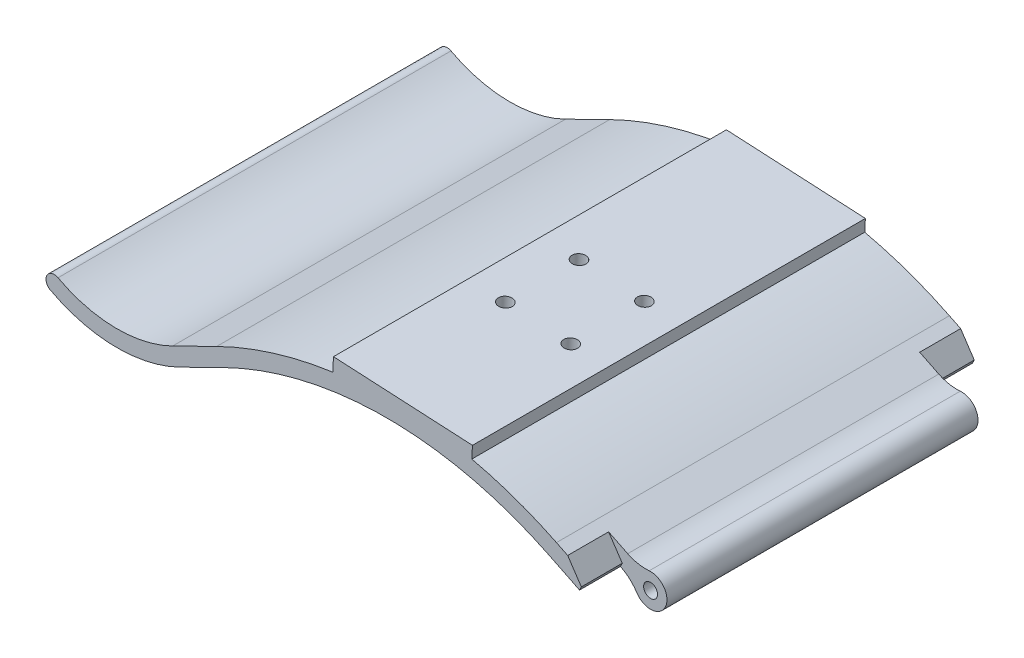
SolidWorks part; units mm, degrees
material "ABS"
ref_plane "Front" through (0, 0, 0) normal (0, 0, 1) x (1, 0, 0)
ref_plane "Top" through (0, 0, 0) normal (0, 1, 0) x (1, 0, 0)
ref_plane "Right" through (0, 0, 0) normal (1, 0, 0) x (0, 0, -1)
sketch "Croquis1" plane through (0, 0, 0) normal (0, 0, 1) x (1, 0, 0)
  line L0 (-39.7374, -9.2477) -> (-50.5044, -14.546)
  line L4 (-80.2705, -10.5153) -> (-82.1489, -14.0467) construction
  line L5 (0, 0) -> (33.2564, 0) construction
  line L6 (0, 22.0797) -> (0, 0) construction
  line L9 (-41.5035, -5.6587) -> (-52.2705, -10.957)
  line L10 (-41.5035, -5.6587) -> (-39.7374, -9.2477) construction
  line L11 (41.5035, -5.6587) -> (39.7374, -9.2477) construction
  line L12 (52.2705, -10.957) -> (50.5044, -14.546) construction
  line L13 (41.5035, -5.6587) -> (52.2705, -10.957)
  line L14 (39.7374, -9.2477) -> (50.5044, -14.546)
  line L15 (-80.2705, -10.5153) -> (-96.9406, -1.6482) construction
  circle A8 centre (54.4956, -14.281) radius 1.7
  arc A12 (52.2705, -10.957) -> (50.5044, -14.546) centre (54.4956, -14.281) cw
  arc A14 (-41.5035, -5.6587) -> (41.5035, -5.6587) centre (0, -90) cw
  arc A15 (-39.7374, -9.2477) -> (39.7374, -9.2477) centre (0, -90) cw
  arc A16 (-52.2705, -10.957) -> (-80.2705, -10.5153) centre (-65.839, 16.6161) cw
  arc A17 (-50.5044, -14.546) -> (-82.1489, -14.0467) centre (-65.839, 16.6161) cw
  arc A18 (-80.2705, -10.5153) -> (-82.1489, -14.0467) centre (-81.2097, -12.281) ccw
  dimension "D1" = 4
  dimension "D3" = 3.4
  dimension "D4" = 90
  dimension "D6" = 28
  dimension "D7" = 105
  dimension "D8" = 2
  dimension "D2" = 4
  dimension "D5" = 12
extrude "Saliente-Extruir1" add sketch "Croquis1" along normal mid plane 96
fillet "Redondeo1" radius 10 2 edges at (50.5044, -14.546, 0) (52.2705, -10.957, 0)
sketch "Croquis3" plane through (0, 0, 48) normal (0, 0, 1) x (1, 0, 0)
  line L0 (48.9085, -9.3026) -> (47.1424, -12.8916)
  arc A0 (51.1332, -16.4476) -> (47.1424, -12.8916) centre (42.7271, -21.8641) ccw construction
  arc A1 (48.9085, -9.3026) -> (54.1608, -10.295) centre (53.3238, -0.3301) ccw construction
  arc A2 (51.1332, -16.4476) -> (54.1608, -10.295) centre (54.4956, -14.281) ccw construction
  arc A3 (51.1332, -16.4476) -> (47.1424, -12.8916) centre (42.7271, -21.8641) ccw
  arc A4 (48.9085, -9.3026) -> (54.1608, -10.295) centre (53.3238, -0.3301) ccw
  arc A5 (51.1332, -16.4476) -> (54.1608, -10.295) centre (54.4956, -14.281) ccw
extrude "Cortar-Extruir1" cut sketch "Croquis3" against normal blind 10
mirror "Simetría1" about plane through (0, 0, 0) normal (0, 0, 1) of "Cortar-Extruir1"
chamfer "Chaflán1" distance 3 angle 60 2 edges at (48.9085, -9.3026, -43) (48.9085, -9.3026, 43)
sketch "Croquis5" plane through (0, 0, 0) normal (0, 0, 1) x (1, 0, 0)
  line L0 (0, 0) -> (0, 20.2507) construction
  line L1 (-12.9767, 6.4407) -> (20.9767, 4.6613)
  line L2 (20.9767, 4.6613) -> (20.8197, 1.6654)
  line L3 (-12.9767, 6.4407) -> (-13.1531, 3.0752)
  line L4 (4, 5.551) -> (4, 35.078) construction
  arc A0 (41.5035, -5.6587) -> (-41.5035, -5.6587) centre (0, -90) ccw construction
  arc A1 (-13.1531, 3.0752) -> (20.8197, 1.6654) centre (0, -90) cw
  dimension "D1" = 93
  dimension "D2" = 4
  dimension "D3" = 3
  dimension "D4" = 34
extrude "Saliente-Extruir2" add sketch "Croquis5" along normal through all and the other way through all
sketch "Croquis6" plane through (0.3011, 5.7448, 0) normal (0.0523, 0.9986, 0) x (0.9986, -0.0523, 0)
  line L0 (20.704, -48) -> (-13.296, -48) construction
  line L1 (-4.296, -15) -> (11.704, -15) construction
  line L2 (-4.296, -15) -> (-4.296, 3) construction
  line L3 (-4.296, 3) -> (11.704, 3) construction
  line L4 (11.704, -15) -> (11.704, 3) construction
  line L5 (-4.296, -15) -> (11.704, 3) construction
  line L6 (-4.296, 3) -> (11.704, -15) construction
  circle A0 centre (-4.296, 3) radius 1.7
  circle A1 centre (11.704, 3) radius 1.7
  circle A2 centre (11.704, -15) radius 1.7
  circle A3 centre (-4.296, -15) radius 1.7
  point P0 (3.704, -48)
  point P13 (3.704, -6)
  dimension "D1" = 3.4
  dimension "D2" = 18
  dimension "D3" = 16
  dimension "D4" = 6
extrude "Cortar-Extruir3" cut sketch "Croquis6" against normal up to next
ref_plane "Plano1" through (0.1441, 2.7489, 0) normal (0.0523, 0.9986, 0) x (0.9986, -0.0523, 0)
sketch "Croquis7" plane through (0.1441, 2.7489, 0) normal (0.0523, 0.9986, 0) x (0.9986, -0.0523, 0)
  line L1 (-0.8896, 3) -> (-2.5928, 5.95)
  line L2 (-2.5928, 5.95) -> (-5.9992, 5.95)
  line L3 (-5.9992, 5.95) -> (-7.7024, 3)
  line L4 (-7.7024, 3) -> (-5.9992, 0.05)
  line L5 (-5.9992, 0.05) -> (-2.5928, 0.05)
  line L6 (-2.5928, 0.05) -> (-0.8896, 3)
  line L7 (15.1104, 3) -> (13.4072, 5.95)
  line L8 (13.4072, 5.95) -> (10.0008, 5.95)
  line L9 (10.0008, 5.95) -> (8.2976, 3)
  line L10 (8.2976, 3) -> (10.0008, 0.05)
  line L11 (10.0008, 0.05) -> (13.4072, 0.05)
  line L12 (13.4072, 0.05) -> (15.1104, 3)
  line L13 (-0.8896, -15) -> (-2.5928, -12.05)
  line L14 (-2.5928, -12.05) -> (-5.9992, -12.05)
  line L15 (-5.9992, -12.05) -> (-7.7024, -15)
  line L16 (-7.7024, -15) -> (-5.9992, -17.95)
  line L17 (-5.9992, -17.95) -> (-2.5928, -17.95)
  line L18 (-2.5928, -17.95) -> (-0.8896, -15)
  line L19 (15.1104, -15) -> (13.4072, -12.05)
  line L20 (13.4072, -12.05) -> (10.0008, -12.05)
  line L21 (10.0008, -12.05) -> (8.2976, -15)
  line L22 (8.2976, -15) -> (10.0008, -17.95)
  line L23 (10.0008, -17.95) -> (13.4072, -17.95)
  line L24 (13.4072, -17.95) -> (15.1104, -15)
  circle A0 centre (-4.296, 3) radius 2.95 construction
  circle A1 centre (11.704, 3) radius 2.95 construction
  circle A2 centre (-4.296, -15) radius 2.95 construction
  circle A3 centre (11.704, -15) radius 2.95 construction
  dimension "D1" = 5.9
extrude "Cortar-Extruir4" cut sketch "Croquis7" against normal up to next
